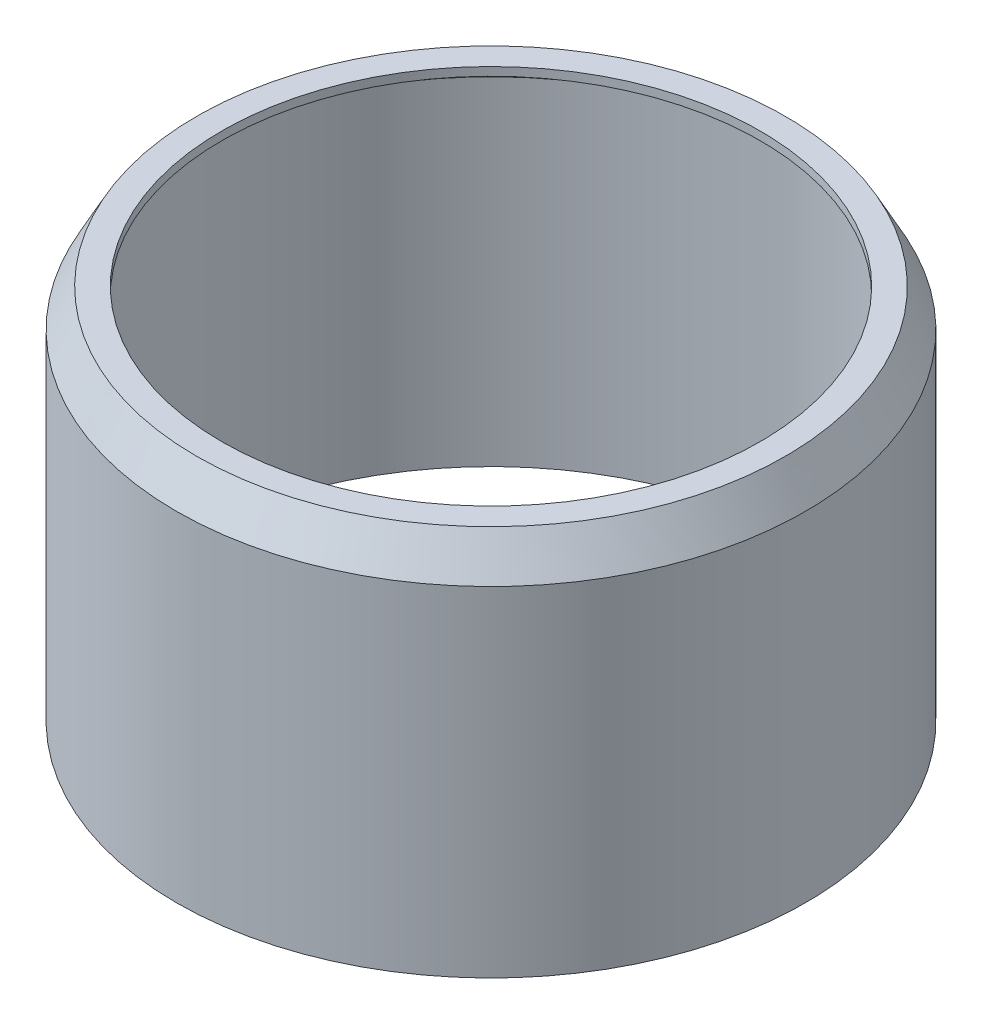
SolidWorks part; units mm, degrees
ref_plane "前视基准面" through (0, 0, 0) normal (0, 0, 1) x (1, 0, 0)
ref_plane "上视基准面" through (0, 0, 0) normal (0, 1, 0) x (1, 0, 0)
ref_plane "右视基准面" through (0, 0, 0) normal (1, 0, 0) x (0, 0, -1)
sketch "草图1" plane through (0, 0, 0) normal (0, 1, 0) x (1, 0, 0)
  circle A0 centre (0, 0) radius 35
  circle A1 centre (0, 0) radius 32
  dimension "D1" = 70
extrude "凸台-拉伸1" add sketch "草图1" along normal blind 1
sketch "草图2" plane through (0, 0, 0) normal (0, 0, 1) x (1, 0, 0)
  line L0 (35, 1) -> (37.3952, -3.4703)
  line L1 (37.3952, -3.4703) -> (37.3952, -43.7717)
  line L2 (37.3952, -43.7717) -> (37.0727, -43.7717)
  line L3 (37.0727, -43.7717) -> (37.0727, -3.6431)
  line L4 (37.0727, -3.6431) -> (35, 0.5497)
  line L5 (35, 0) -> (35, 1) construction
  line L6 (35, 0.5497) -> (35, 1)
  line L7 (0, 0) -> (0, -20.1529) construction
  point P12 (0, 0)
revolve "旋转1" add sketch "草图2" angle 360 about L7
